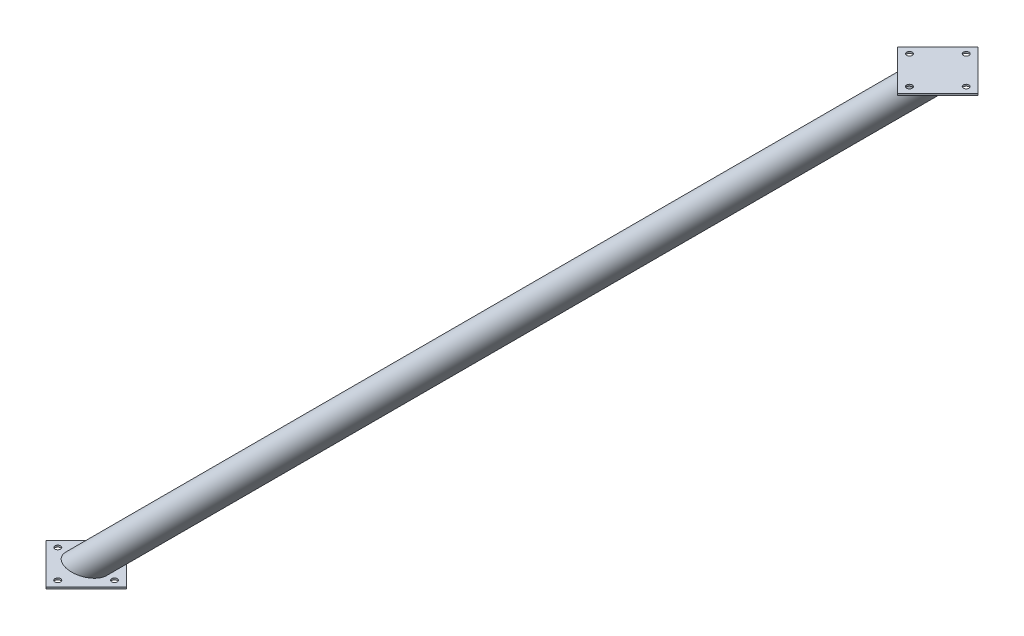
SolidWorks part; units mm, degrees
ref_plane "Alzado" through (0, 0, 0) normal (0, 0, 1) x (1, 0, 0)
ref_plane "Planta" through (0, 0, 0) normal (0, 1, 0) x (1, 0, 0)
ref_plane "Vista lateral" through (0, 0, 0) normal (1, 0, 0) x (0, 0, -1)
sketch "Croquis1" plane through (0, 0, 0) normal (0, 0, 1) x (1, 0, 0)
  line L1 (1500, 1500) -> (1500, 0) construction
  line L2 (0, 0) -> (1500, 0) construction
  line L14 (1500, 1500) -> (1517.9605, 1482.0395) construction
  line L16 (1517.9605, 1482.0395) -> (1535.921, 1500) construction
  line L19 (1535.921, 1500) -> (1534.5068, 1501.4142) construction
  line L20 (1500, 1500) -> (0, 0) construction
  line L21 (1500, 1500) -> (1535.921, 1500) construction
  line L22 (1535.921, 1500) -> (0, -35.921)
  line L25 (1534.5068, 1501.4142) -> (1535.921, 1500)
  line L27 (0, 0) -> (-17.9605, -17.9605) construction
  line L29 (-35.921, 0) -> (0, -35.921) construction
  line L30 (-1.4142, -34.5068) -> (0, -35.921) construction
  line L31 (1534.5068, 1501.4142) -> (-1.4142, -34.5068)
  line L32 (-1.4142, -34.5068) -> (0, -35.921)
  line L33 (0, 0) -> (-35.921, 0) construction
  point P6 (750, 750)
  point P9 (1249.9999, 1249.9999)
  dimension "D1" = 1500
  dimension "D2" = 1500
  dimension "D3" = 90
  dimension "D4" = 90
  dimension "D5" = 25.4
  dimension "D6" = 50.8
  dimension "D7" = 2
  dimension "D8" = 90
  dimension "D9" = 45
  dimension "D10" = 90
  dimension "D11" = 707.1067
revolve "Revolución1" add sketch "Croquis1" angle 360 about L20
sketch "Croquis2" plane through (0, 0, 0) normal (0, 0, 1) x (1, 0, 0)
  line L0 (-35.921, 0) -> (35.921, 0)
  line L1 (0, -35.921) -> (1535.921, 1500) construction
  line L2 (35.921, 0) -> (0, -35.921)
  line L3 (0, -35.921) -> (-35.921, 0)
  line L4 (1535.921, 1500) -> (1464.079, 1500)
  line L5 (1500, 1535.921) -> (-35.921, 0) construction
  line L6 (1464.079, 1500) -> (1500, 1535.921)
  line L7 (1500, 1535.921) -> (1535.921, 1500)
extrude "Cortar-Extruir1" cut sketch "Croquis2" against normal through all and the other way through all contours L3 L0 L2 | L7 L4 L6
sketch "Croquis7" plane through (0, 0, 0) normal (0, -1, 0) x (1, 0, 0)
  circle A0 centre (35.921, 0) radius 6.9357
  ellipse E0 centre (0, 0) end of major axis (35.921, 0) minor radius 25.4 construction
sketch "Croquis3" plane through (0, 0, 0) normal (0, -1, 0) x (1, 0, 0)
  line L0 (-70.7107, 0) -> (0, 70.7107)
  line L5 (50, 0) -> (-50, 0) construction
  line L6 (0, 50) -> (0, -50) construction
  line L7 (0, -70.7107) -> (-70.7107, 0)
  line L8 (70.7107, 0) -> (0, -70.7107)
  line L9 (0, 70.7107) -> (70.7107, 0)
  line L10 (0, 0) -> (147.1093, 0) construction
  circle A5 centre (0, 0) radius 50 construction
  circle A6 centre (-50, 0) radius 5
  circle A7 centre (0, 50) radius 5
  circle A8 centre (50, 0) radius 5
  circle A9 centre (0, -50) radius 5
  point P0 (0, 0)
  point P7 (0, 0)
  point P11 (0, 0)
  point P12 (-35.3553, 35.3553)
  point P19 (0, 0)
  point P22 (-35.3553, -35.3553)
  point P26 (35.3553, -35.3553)
  point P29 (35.3553, 35.3553)
  point P30 (0, 0)
  dimension "D3" = 70.7107
  dimension "D4" = 100
  dimension "D6" = 10
  dimension "D1" = 100
  dimension "D2" = 45
  dimension "D5" = 100
  dimension "D7" = 4
extrude "Saliente-Extruir1" add sketch "Croquis3" along normal blind 3
ref_plane "Plano1" through (0, 750, 0) normal (0, 1, 0) x (1, 0, 0)
ref_plane "Plano2" through (707.11, 0, 0) normal (1, 0, 0) x (0, 0, -1)
sketch "Croquis6" plane through (0, 0, 0) normal (0, 0, 1) x (1, 0, 0)
  point P0 (35.921, 0)
sketch "Croquis9" plane through (0, 1500, 0) normal (0, 1, 0) x (1, 0, 0)
  line L0 (1429.2893, 0) -> (1500, 70.7107)
  line L1 (1550, 0) -> (1450, 0) construction
  line L2 (1500, 50) -> (1500, -50) construction
  line L3 (1500, -70.7107) -> (1429.2893, 0)
  line L4 (1570.7107, 0) -> (1500, -70.7107)
  line L5 (1500, 70.7107) -> (1570.7107, 0)
  line L6 (1500, 0) -> (1466.9074, 0) construction
  circle A0 centre (1500, 0) radius 50 construction
  circle A1 centre (1500, 50) radius 5
  circle A2 centre (1550, 0) radius 5
  circle A3 centre (1500, -50) radius 5
  circle A4 centre (1450, 0) radius 5
  ellipse E0 centre (1500, 0) end of major axis (1533.0926, 0) minor radius 23.4 construction
  point P4 (1500, 0)
  point P8 (1500, 0)
  point P9 (1464.6447, 35.3553)
  point P12 (1464.6447, -35.3553)
  point P16 (1535.3553, -35.3553)
  point P17 (1535.3553, 35.3553)
  point P36 (1500, 0)
  ellipse M6 centre (1500, 0) end of major axis (1535.921, 0) minor radius 25.4
  ellipse M7 centre (1500, 0) end of major axis (1533.0926, 0) minor radius 23.4
  dimension "D3" = 10
  dimension "D1" = 100
  dimension "D2" = 100
  dimension "D4" = 45
  dimension "D5" = 4
extrude "Saliente-Extruir5" add sketch "Croquis9" along normal blind 3 contours L5 L0 L3 L4 A4 A3 A2 A1 M6 | M7 | M6 M7
ref_plane "Plano3" through (0, 0, 0) normal (-0.7071, 0.7071, 0) x (-0.7071, -0.7071, 0)
sketch "Croquis10" plane through (0, 0, 0) normal (-0.7071, 0.7071, 0) x (-0.7071, -0.7071, 0)
  line L0 (-1060.6602, 0) -> (-1060.6602, 796.0438) construction
  line L1 (-2146.7203, 0) -> (25.4, 0) construction
